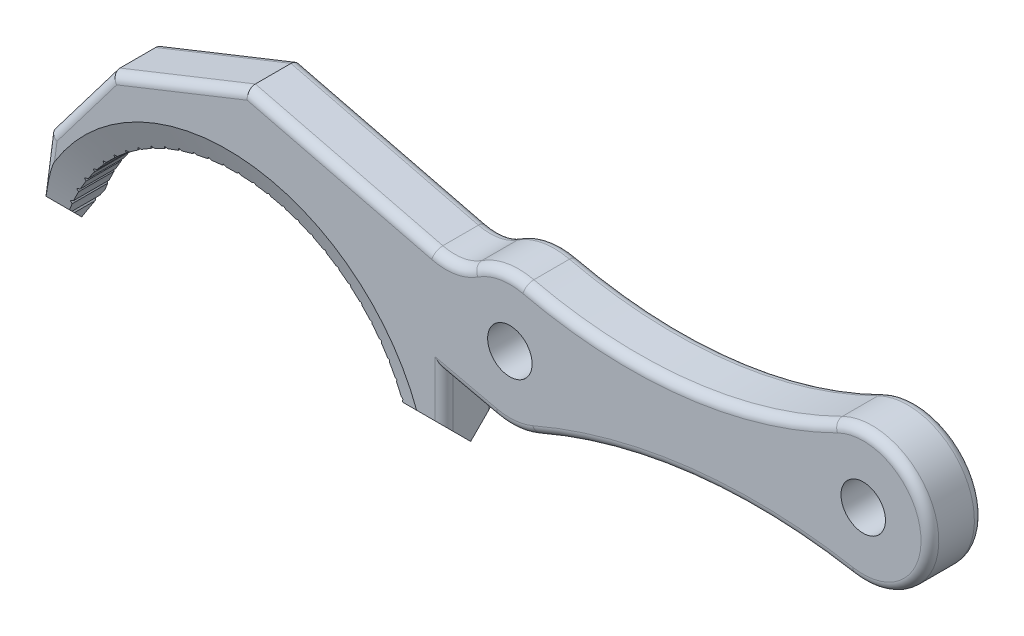
SolidWorks part; units mm, degrees
ref_plane "Front Plane" through (0, 0, 0) normal (0, 0, 1) x (1, 0, 0)
ref_plane "Top Plane" through (0, 0, 0) normal (0, 1, 0) x (1, 0, 0)
ref_plane "Right Plane" through (0, 0, 0) normal (1, 0, 0) x (0, 0, -1)
sketch "Sketch1" plane through (0, 0, 0) normal (0, 0, 1) x (1, 0, 0)
  line L0 (0, 0) -> (50000, 0) construction
  line L1 (24.5934, 0) -> (30.9434, 0)
  line L2 (30.9434, 0) -> (30.9434, 10.16)
  line L3 (30.9434, 10.16) -> (38.2289, 8.4945)
  line L4 (-24.5934, 0) -> (-27.0775, 0)
  line L5 (-27.0775, 0) -> (-25.5277, 11.9038)
  line L6 (-25.5277, 11.9038) -> (-16.5858, 23.6869)
  line L7 (-16.5858, 23.6869) -> (2.7457, 31.3837)
  line L8 (2.7457, 31.3837) -> (29.5138, 24.765)
  line L10 (0, 0) -> (-25.5277, 11.9038) construction
  line L11 (0, 0) -> (-16.5858, 23.6869) construction
  line L12 (0, 0) -> (2.7457, 31.3837) construction
  line L13 (0, 0) -> (29.5138, 24.765) construction
  line L14 (40.3515, 17.78) -> (49369.6595, 5769.7165) construction
  circle A0 centre (0, -6.35) radius 25.4 construction
  arc A1 (24.5934, 0) -> (-24.5934, 0) centre (0, -6.35) ccw
  circle A3 centre (40.3515, 17.78) radius 9.525 construction
  circle A4 centre (40.3515, 17.78) radius 3.175
  circle A5 centre (90.8097, 23.6636) radius 9.525 construction
  circle A6 centre (90.8097, 23.6636) radius 3.175
  arc A7 (86.5736, 32.1948) -> (89.1398, 14.2861) centre (90.8097, 23.6636) cw
  arc A10 (86.5736, 32.1948) -> (42.5111, 27.057) centre (57.3893, 90.971) cw
  arc A11 (89.1398, 14.2861) -> (44.1342, 9.0383) centre (75.3564, -63.1167) ccw
  arc A12 (29.5138, 24.765) -> (35.1023, 25.728) centre (31.2093, 31.6224) ccw
  arc A13 (35.1023, 25.728) -> (42.5111, 27.057) centre (40.3515, 17.78) cw
  arc A14 (44.1342, 9.0383) -> (38.2289, 8.4945) centre (40.3515, 17.78) cw
  dimension "D2" = 50.8
  dimension "D7" = 19.05
  dimension "D9" = 6.35
  dimension "D10" = 6.35
  dimension "D1" = 6.35
  dimension "D3" = 25
  dimension "D4" = 30
  dimension "D5" = 40
  dimension "D6" = 45
  dimension "D8" = 17.78
  dimension "D11" = 10.16
  dimension "D12" = 50.8
extrude "Boss-Extrude1" add sketch "Sketch1" along normal mid plane 7.62
sketch "Sketch2" plane through (0, 0, 0) normal (1, 0, 0) x (0, 0, -1)
  line L0 (0, 0) -> (3.81, 3.81)
  line L1 (3.81, 0) -> (3.81, 10.16) construction
  line L2 (3.81, 3.81) -> (3.81, 0)
  line L3 (3.81, 0) -> (0, 0)
  dimension "D1" = 45
extrude "Cut-Extrude1" cut sketch "Sketch2" against normal through all both and the other way through all
mirror "Mirror1" about plane through (0, 0, 0) normal (0, 0, 1) of "Cut-Extrude1"
chamfer "Chamfer1" distance 1.27 angle 70 2 edges at (0, 19.05, -3.81) (0, 19.05, 3.81)
sketch "Sketch4" plane through (0, 0, 3.81) normal (0, 0, 1) x (1, 0, 0)
  line L3 (23.939, 3.0395) -> (22.0842, -0.4453)
  line L4 (22.0842, -0.4453) -> (20.2096, 4.3341)
  line L5 (20.2096, 4.3341) -> (23.939, 3.0395)
  circle A0 centre (0, -6.35) radius 22.86 construction
  arc A1 (23.7934, 2.54) -> (-23.7934, 2.54) centre (0, -6.35) ccw construction
  dimension "D1" = 2.54
extrude "Cut-Extrude2" cut sketch "Sketch4" against normal through all
pattern_circular "CirPattern1" count 30 over 140 about axis through (0, -6.35, 0) along (0, 0, 1) of "Cut-Extrude2"
fillet "Fillet1" radius 1.27 24 edges at (34.5861, 9.3273, -3.81) (41.2249, 8.2951, -3.81) (66.2507, 14.9746, -3.81) (100.2384, 25.0146, -3.81) (16.1297, 28.0743, -3.81) (32.4089, 24.6611, -3.81) (38.6698, 27.1554, -3.81) (34.5861, 9.3273, 3.81) (41.2249, 8.2951, 3.81) (66.2507, 14.9746, 3.81) (100.2384, 25.0146, 3.81) (16.1297, 28.0743, 3.81) (32.4089, 24.6611, 3.81) (38.6698, 27.1554, 3.81) (30.9434, 6.985, -3.81) (30.9434, 6.985, 3.81) (64.9897, 25.7897, -3.81) (64.9897, 25.7897, 3.81) (-25.9475, 8.6794, -3.81) (-25.9475, 8.6794, 3.81) (-21.0568, 17.7954, 3.81) (-21.0568, 17.7954, -3.81) (-6.92, 27.5353, -3.81) (-6.92, 27.5353, 3.81)
